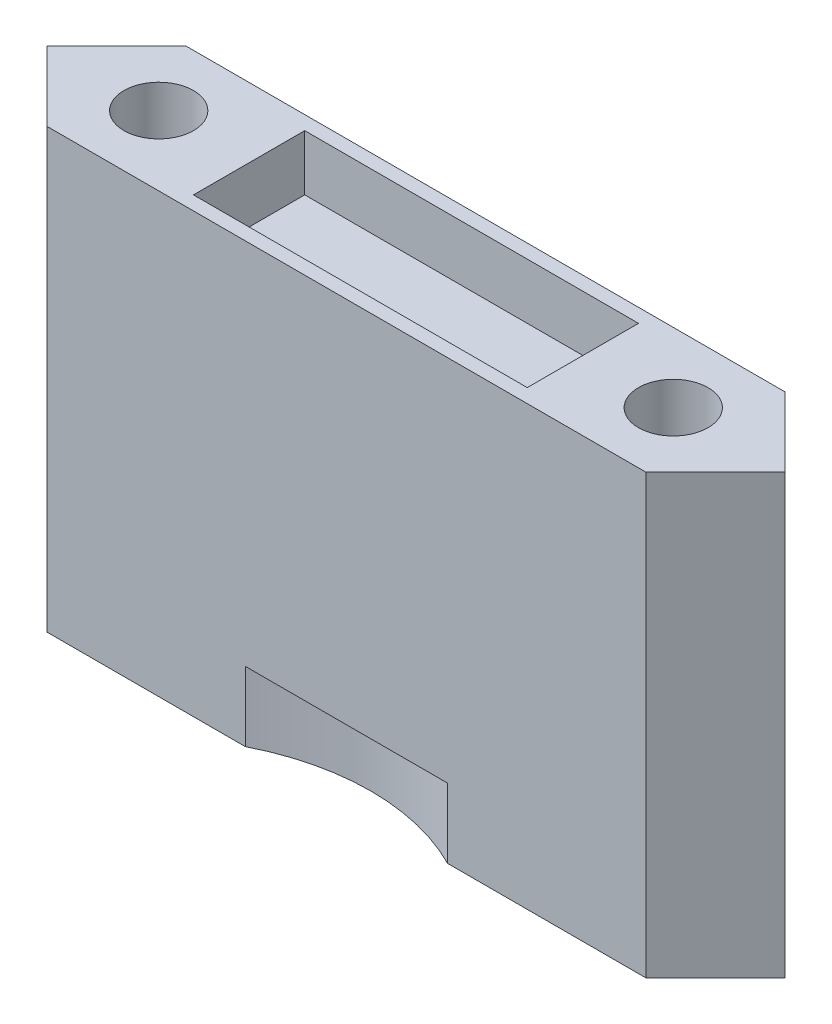
SolidWorks part; units mm, degrees
ref_plane "Front Plane" through (0, 0, 0) normal (0, 0, 1) x (1, 0, 0)
ref_plane "Top Plane" through (0, 0, 0) normal (0, 1, 0) x (1, 0, 0)
ref_plane "Right Plane" through (0, 0, 0) normal (1, 0, 0) x (0, 0, -1)
sketch "Sketch1" plane through (0, 0, 0) normal (0, 1, 0) x (1, 0, 0)
  line L0 (20.828, 0) -> (-20.828, 0) construction
  line L1 (-27.3588, 6.35) -> (-33.7088, 0)
  line L2 (27.3588, -6.35) -> (-27.3588, -6.35)
  line L3 (0, 6.35) -> (0, -6.35) construction
  line L4 (27.3588, 6.35) -> (-27.3588, 6.35)
  line L5 (33.7088, 0) -> (27.3588, -6.35)
  line L6 (27.3588, -6.35) -> (-27.3588, 6.35) construction
  line L7 (27.3588, 6.35) -> (-27.3588, -6.35) construction
  line L8 (-33.7088, 0) -> (-27.3588, -6.35)
  line L9 (27.3588, 6.35) -> (33.7088, 0)
  circle A0 centre (-23.495, 0) radius 2.667 construction
  circle A1 centre (23.495, 0) radius 2.667 construction
  circle A2 centre (-23.495, 0) radius 3.175
  circle A3 centre (23.495, 0) radius 3.175
  point P4 (0, 0)
  point P8 (0, 0)
  dimension "D1" = 5.334
  dimension "D5" = 6.35
  dimension "D2" = 41.656
  dimension "D3" = 12.7
  dimension "D4" = 45
extrude "Boss-Extrude1" add sketch "Sketch1" along normal blind 40
sketch "Sketch2" plane through (0, 40, 0) normal (0, 1, 0) x (1, 0, 0)
  line L1 (15.24, -5.08) -> (-15.24, -5.08)
  line L2 (15.24, -5.08) -> (15.24, 5.08)
  line L3 (15.24, 5.08) -> (-15.24, 5.08)
  line L4 (-15.24, -5.08) -> (-15.24, 5.08)
  line L5 (15.24, -5.08) -> (-15.24, 5.08) construction
  line L6 (15.24, 5.08) -> (-15.24, -5.08) construction
  point P0 (0, 0)
  dimension "D1" = 30.48
  dimension "D2" = 10.16
extrude "Cut-Extrude1" cut sketch "Sketch2" against normal blind 5.08
sketch "Sketch3" plane through (0, 0, 0) normal (0, -1, 0) x (-1, 0, 0)
  circle A0 centre (0, -24.4501) radius 19.05 construction
  circle A1 centre (-23.495, 0) radius 3.175 construction
  circle A2 centre (0, -24.4501) radius 20.32
  dimension "D1" = 38.1
  dimension "D2" = 11.684
  dimension "D3" = 40.64
extrude "Cut-Extrude2" cut sketch "Sketch3" against normal blind 6.35
